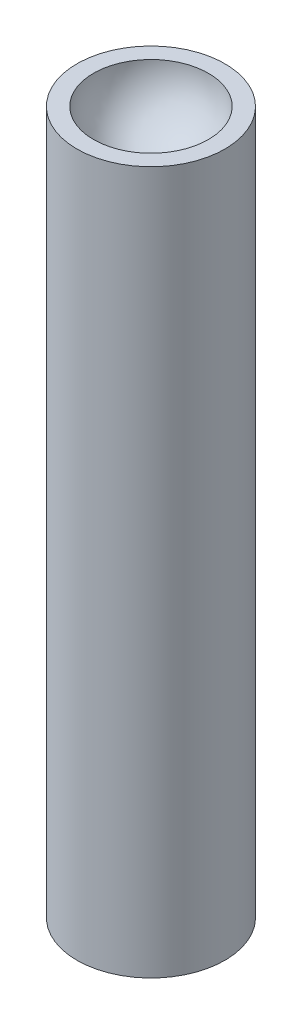
SolidWorks part; units mm, degrees
ref_plane "Front Plane" through (0, 0, 0) normal (0, 0, 1) x (1, 0, 0)
ref_plane "Top Plane" through (0, 0, 0) normal (0, 1, 0) x (1, 0, 0)
ref_plane "Right Plane" through (0, 0, 0) normal (1, 0, 0) x (0, 0, -1)
sketch "Sketch1" plane through (0, 0, 0) normal (0, 1, 0) x (1, 0, 0)
  circle A0 centre (0, 0) radius 2
  dimension "D1" = 4
extrude "Boss-Extrude1" add sketch "Sketch1" along normal blind 19
sketch "Sketch3" plane through (0, 19, 0) normal (0, 1, 0) x (1, 0, 0)
  line L0 (0, 1.5535) -> (0, -1.5535)
  arc A0 (0, 1.5535) -> (0, -1.5535) centre (0, 0) ccw
revolve "Cut-Revolve2" cut sketch "Sketch3" angle 360 about L0
